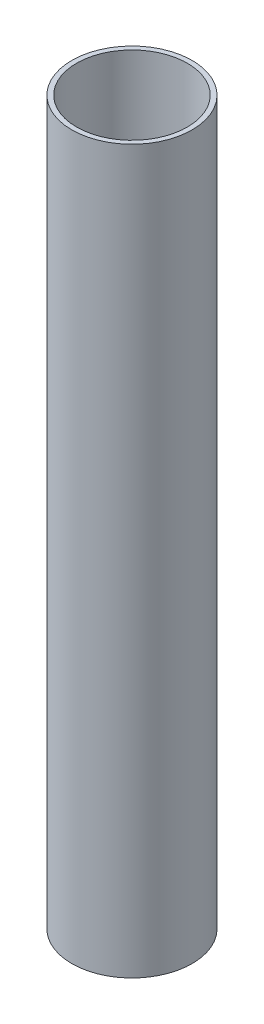
SolidWorks part; units mm, degrees
material "1060 Сплав"
ref_plane "Спереди" through (0, 0, 0) normal (0, 0, 1) x (1, 0, 0)
ref_plane "Сверху" through (0, 0, 0) normal (0, 1, 0) x (1, 0, 0)
ref_plane "Справа" through (0, 0, 0) normal (1, 0, 0) x (0, 0, -1)
sketch "Эскиз1" plane through (0, 0, 0) normal (0, 1, 0) x (1, 0, 0)
  circle A0 centre (0, 0) radius 11.5
  circle A1 centre (0, 0) radius 12.5
  dimension "D1" = 23
  dimension "D2" = 1
extrude "Бобышка-Вытянуть1" add sketch "Эскиз1" along normal blind 150
